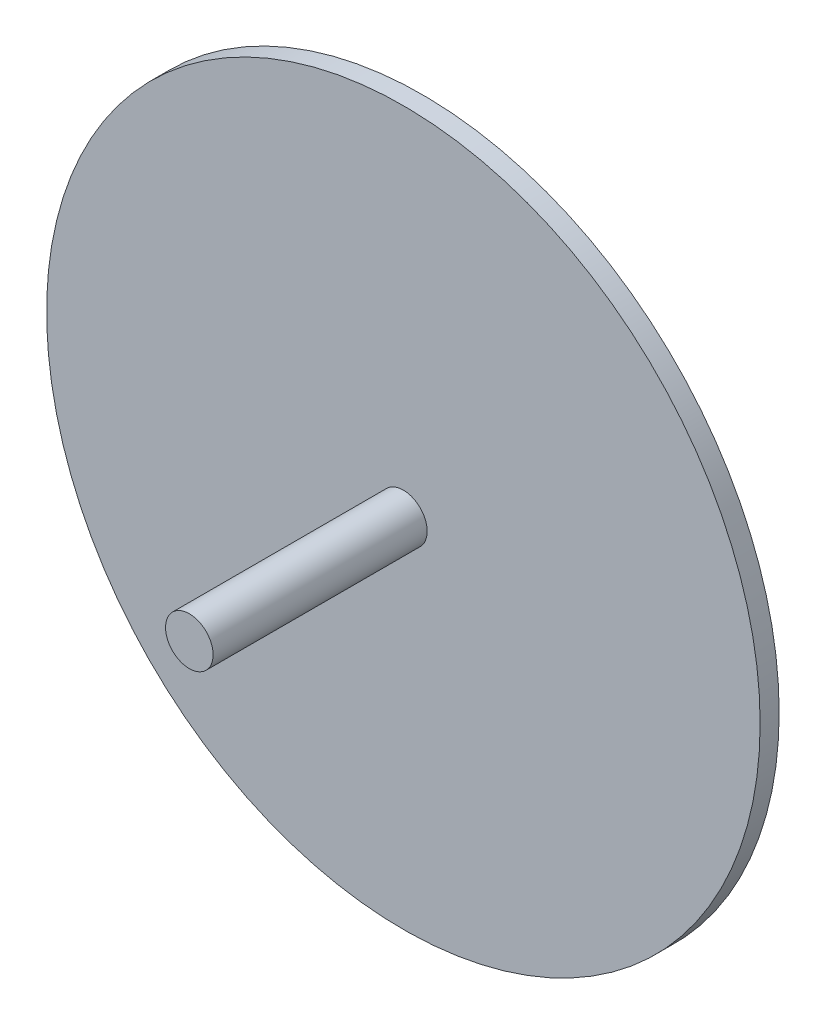
SolidWorks part; units mm, degrees
material "AISI 304"
ref_plane "Front Plane" through (0, 0, 0) normal (0, 0, 1) x (1, 0, 0)
ref_plane "Top Plane" through (0, 0, 0) normal (0, 1, 0) x (1, 0, 0)
ref_plane "Right Plane" through (0, 0, 0) normal (1, 0, 0) x (0, 0, -1)
sketch "Sketch2" plane through (0, 0, 0) normal (0, 0, 1) x (1, 0, 0)
  circle A0 centre (0, 0) radius 75
  dimension "D1" = 150
extrude "Boss-Extrude1" add sketch "Sketch2" along normal blind 4
sketch "Sketch3" plane through (0, 0, 4) normal (0, 0, 1) x (1, 0, 0)
  circle A0 centre (0, 0) radius 5
  dimension "D1" = 10
extrude "Boss-Extrude2" add sketch "Sketch3" along normal blind 45
